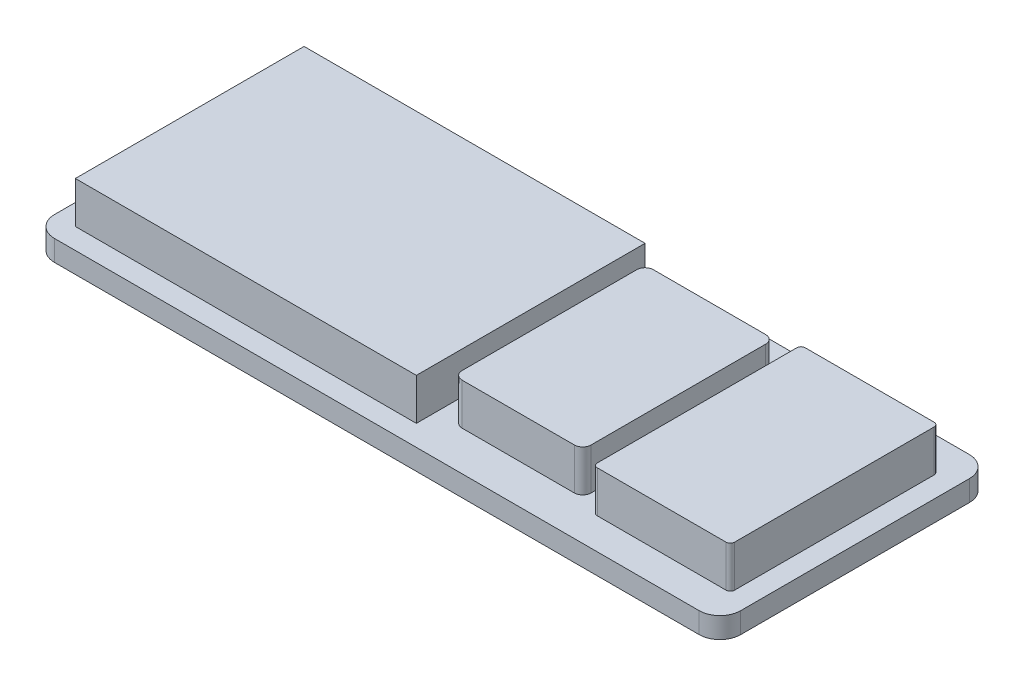
SolidWorks part; units mm, degrees
ref_plane "Front Plane" through (0, 0, 0) normal (0, 0, 1) x (1, 0, 0)
ref_plane "Top Plane" through (0, 0, 0) normal (0, 1, 0) x (1, 0, 0)
ref_plane "Right Plane" through (0, 0, 0) normal (1, 0, 0) x (0, 0, -1)
sketch "Sketch1" plane through (0, 0, 0) normal (0, 1, 0) x (1, 0, 0)
  line L13 (-65.0251, 32.5) -> (99.9749, 32.5)
  line L14 (-65.0251, 32.5) -> (-65.0251, -32.5)
  line L15 (-65.0251, -32.5) -> (99.9749, -32.5)
  line L16 (99.9749, 32.5) -> (99.9749, -32.5)
  dimension "D12" = 65
  dimension "D13" = 32.5
  dimension "D14" = 165
extrude "Boss-Extrude1" add sketch "Sketch1" along normal blind 5
fillet "Fillet1" radius 5 4 edges at (-65.0251, 2.5, -32.5) (99.9749, 2.5, -32.5) (99.9749, 2.5, 32.5) (-65.0251, 2.5, 32.5)
sketch "Sketch2" plane through (0, 5, 0) normal (0, 1, 0) x (1, 0, 0)
  line L0 (-60.0251, 27.5) -> (21.9749, 27.5)
  line L1 (-60.0251, 27.5) -> (-60.0251, -27.5)
  line L2 (-60.0251, -27.5) -> (21.9749, -27.5)
  line L3 (21.9749, 27.5) -> (21.9749, -27.5)
  line L4 (26.4749, 23) -> (57.4749, 23)
  line L5 (26.4749, 23) -> (26.4749, -23)
  line L6 (26.4749, -23) -> (57.4749, -23)
  line L7 (57.4749, 23) -> (57.4749, -23)
  line L8 (61.9749, 25) -> (94.9749, 25)
  line L9 (61.9749, 25) -> (61.9749, -25)
  line L10 (61.9749, -25) -> (94.9749, -25)
  line L11 (94.9749, 25) -> (94.9749, -25)
  line L12 (-65.0251, 27.5) -> (-65.0251, -27.5) construction
  line L13 (94.9749, 32.5) -> (-60.0251, 32.5) construction
  line L14 (99.9749, -27.5) -> (99.9749, 27.5) construction
  dimension "D1" = 31
  dimension "D2" = 46
  dimension "D3" = 50
  dimension "D4" = 55
  dimension "D5" = 82
  dimension "D6" = 5
  dimension "D7" = 5
  dimension "D8" = 5
  dimension "D9" = 25
  dimension "D10" = 23
  dimension "D11" = 4.5
  dimension "D12" = 4.5
extrude "Boss-Extrude2" add sketch "Sketch2" along normal blind 10
fillet "Fillet2" radius 2 4 edges at (26.4749, 10, -23) (57.4749, 10, -23) (57.4749, 10, 23) (26.4749, 10, 23)
fillet "Fillet3" radius 1 4 edges at (61.9749, 10, -25) (94.9749, 10, -25) (94.9749, 10, 25) (61.9749, 10, 25)
